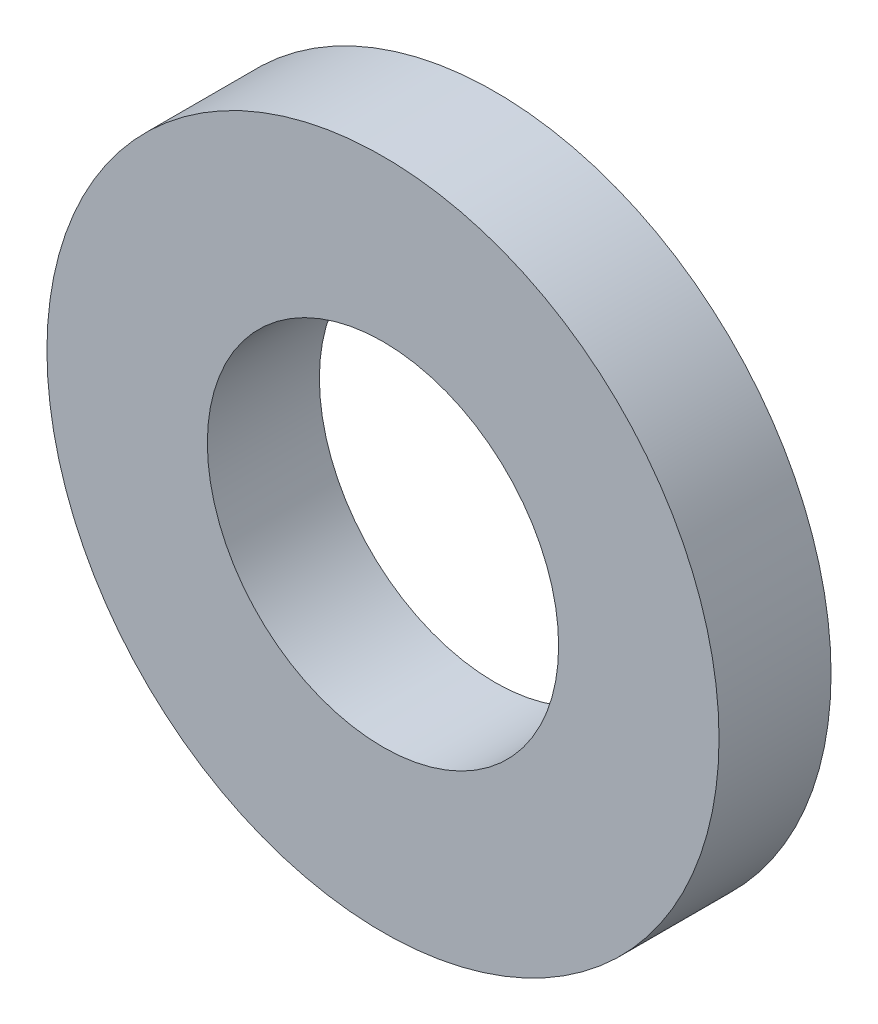
SolidWorks part; units mm, degrees
ref_plane "Front Plane" through (0, 0, 0) normal (0, 0, 1) x (1, 0, 0)
ref_plane "Top Plane" through (0, 0, 0) normal (0, 1, 0) x (1, 0, 0)
ref_plane "Right Plane" through (0, 0, 0) normal (1, 0, 0) x (0, 0, -1)
sketch "Sketch1" plane through (0, 0, 0) normal (0, 0, 1) x (1, 0, 0)
  circle A0 centre (0, 0) radius 9.525
extrude "Boss-Extrude1" add sketch "Sketch1" along normal blind 3.175
sketch "Sketch2" plane through (0, 0, 3.175) normal (0, 0, 1) x (1, 0, 0)
  circle A0 centre (0, 0) radius 4.7625
extrude "Boss-Extrude2" add sketch "Sketch2" along normal blind 4.7498
sketch "Sketch3" plane through (0, 0, 7.9248) normal (0, 0, 1) x (1, 0, 0)
  circle A0 centre (0, 0) radius 4.9784
extrude "Cut-Extrude1" cut sketch "Sketch3" against normal blind 7.9756
